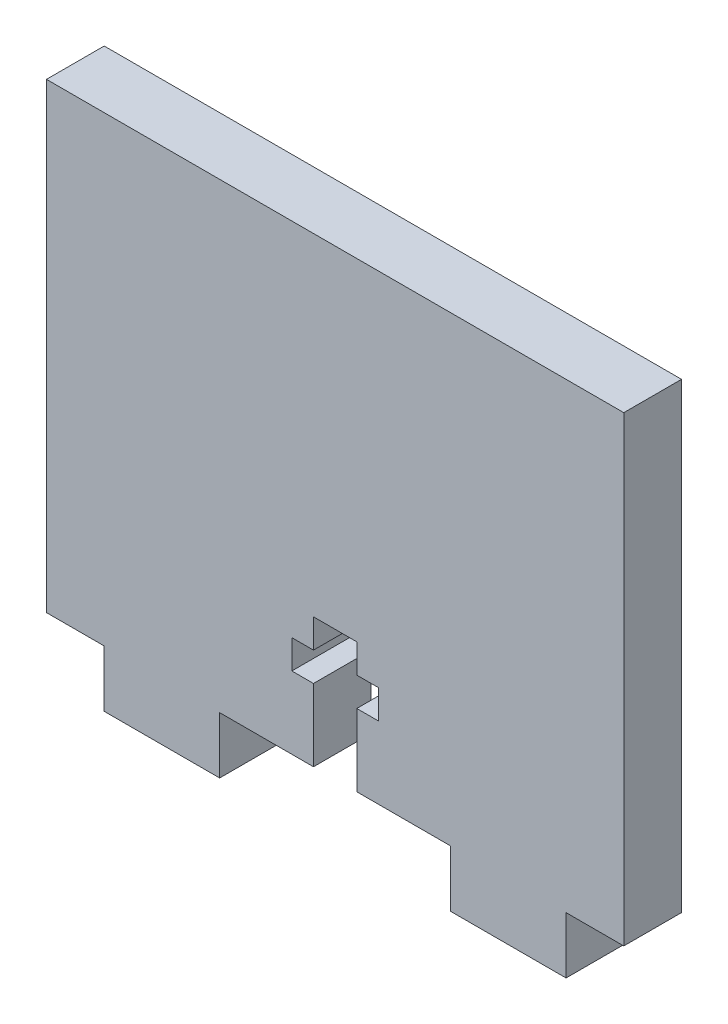
SolidWorks part; units mm, degrees
ref_plane "Front Plane" through (0, 0, 0) normal (0, 0, 1) x (1, 0, 0)
ref_plane "Top Plane" through (0, 0, 0) normal (0, 1, 0) x (1, 0, 0)
ref_plane "Right Plane" through (0, 0, 0) normal (1, 0, 0) x (0, 0, -1)
sketch "Sketch1" plane through (0, 0, 0) normal (0, 0, 1) x (1, 0, 0)
  line L0 (36.5125, 7.9375) -> (36.5125, 11.1125)
  line L1 (0, 0) -> (6.35, 0)
  line L2 (0, 0) -> (0, 50.8)
  line L3 (0, 50.8) -> (63.5, 50.8)
  line L4 (63.5, 0) -> (63.5, 50.8)
  line L5 (34.1313, 0) -> (44.45, 0)
  line L6 (6.35, 0) -> (6.35, -6.2279)
  line L7 (6.35, -6.2279) -> (19.05, -6.2279)
  line L8 (19.05, 0) -> (19.05, -6.2279)
  line L10 (44.45, 0) -> (44.45, -6.2279)
  line L11 (44.45, -6.2279) -> (57.15, -6.2279)
  line L12 (57.15, 0) -> (57.15, -6.2279)
  line L13 (57.15, 0) -> (63.5, 0)
  line L14 (19.05, 0) -> (29.3687, 0)
  line L15 (34.1313, 14.2875) -> (29.3687, 14.2875)
  line L16 (29.3687, 0) -> (29.3687, 7.9375)
  line L20 (29.3687, 0) -> (29.3687, 7.9375)
  line L21 (29.3687, 7.9375) -> (26.9875, 7.9375)
  line L23 (29.3687, 11.1125) -> (26.9875, 11.1125)
  line L24 (26.9875, 7.9375) -> (26.9875, 11.1125)
  line L25 (34.1313, 11.1125) -> (36.5125, 11.1125)
  line L27 (34.1313, 7.9375) -> (36.5125, 7.9375)
  line L28 (34.1313, 0) -> (34.1313, 7.9375)
  line L29 (34.1313, 0) -> (34.1313, 7.9375)
  line L30 (34.1313, 11.1125) -> (34.1313, 14.2875)
  line L31 (29.3687, 11.1125) -> (29.3687, 14.2875)
  dimension "D1" = 12.7
  dimension "D2" = 6.35
  dimension "D3" = 25.4
  dimension "D4" = 12.7
  dimension "D5" = 6.35
  dimension "D6" = 50.8
  dimension "D8" = 2.3813
  dimension "D9" = 3.175
  dimension "D10" = 7.9375
  dimension "D11" = 3.175
extrude "Boss-Extrude1" add sketch "Sketch1" along normal blind 6.35 contours L23 L31 L15 L30 L25 L0 L27 L28 L5 L10 L11 L12 L13 L4 L3 L2 L1 L6 L7 L8 L14 L16 L21 L24
